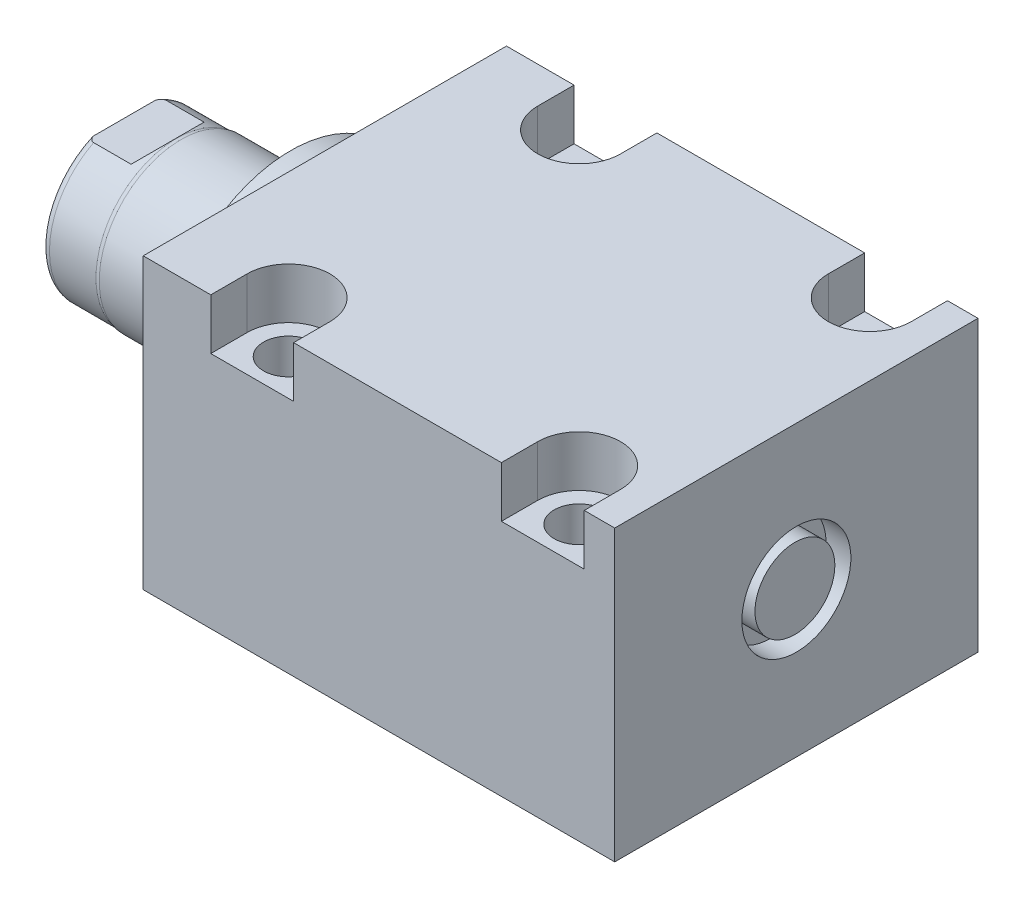
SolidWorks part; units mm, degrees
material "Alloy Steel"
ref_plane "Front Plane" through (0, 0, 0) normal (0, 0, 1) x (1, 0, 0)
ref_plane "Top Plane" through (0, 0, 0) normal (0, 1, 0) x (1, 0, 0)
ref_plane "Right Plane" through (0, 0, 0) normal (1, 0, 0) x (0, 0, -1)
ref_plane "Plane1" through (0, 0, 0) normal (1, 0, 0) x (0, 0, -1)
sketch "Sketch1" plane through (0, 0, 0) normal (1, 0, 0) x (0, 0, -1)
  line L0 (-31.75, 25.146) -> (31.75, 25.146)
  line L1 (31.75, 25.146) -> (31.75, -25.4)
  line L2 (31.75, -25.4) -> (-31.75, -25.4)
  line L3 (-31.75, -25.4) -> (-31.75, 25.146)
  line L4 (0, -24.4475) -> (0, 24.4475) construction
  dimension "D1" = 50.546
  dimension "D2" = 25.4
  dimension "D3" = 63.5
  dimension "D4" = 31.75
extrude "Extrude1" add sketch "Sketch1" along normal blind 82.42
sketch "Sketch5" plane through (0, 0, 0) normal (-1, 0, 0) x (0, 0, 1)
  circle A0 centre (0, 0) radius 22.225
  dimension "D1" = 44.45
extrude "Extrude2" add sketch "Sketch5" along normal blind 5.969
ref_plane "Plane5" through (0, 0, 0) normal (0, -1, 0) x (0, 0, 1)
sketch "Sketch6" plane through (0, 0, 0) normal (0, -1, 0) x (0, 0, 1)
  line L0 (0, 5.969) -> (-14.2875, 5.969)
  line L1 (-14.2875, 5.969) -> (-14.2875, 35.06)
  line L2 (-14.2875, 35.06) -> (0, 35.06)
  line L3 (0, 35.06) -> (0, 5.969)
  line L4 (0, -5.7546) -> (0, 21.1709) construction
  line L5 (22.225, 5.969) -> (-22.225, 5.969) construction
  line L6 (31.75, -82.42) -> (-31.75, -82.42) construction
  dimension "D1" = 117.48
  dimension "D2" = 28.575
revolve "Revolve1" add sketch "Sketch6" angle 360 about L4
ref_plane "Plane6" through (-18.5113, 3.2639, 0) normal (0, 0, 1) x (0, 1, 0)
sketch "S2D0001" plane through (-18.5113, 3.2639, 0) normal (0, 0, 1) x (0, 1, 0)
  line L0 (2.286, 14.481) -> (2.286, -1.9425)
  line L2 (3.4798, 16.5487) -> (-3.2639, 16.5487)
  line L3 (-3.2639, 16.5487) -> (-3.2639, -1.9425)
  line L4 (2.286, 14.481) -> (3.4798, 16.5487)
  line L5 (-3.2639, -18.5113) -> (-3.2639, 2.765) construction
  line L6 (11.0236, 16.5487) -> (-17.5514, 16.5487) construction
  line L7 (2.286, -1.9425) -> (-3.2639, -1.9425)
  dimension "D1" = 30
  dimension "D2" = 13.4874
  dimension "D3" = 11.0998
  dimension "D4" = 18.4912
revolve "Cut-Revolve4" cut sketch "S2D0001" angle 360 about L5
ref_plane "Plane7" through (0, 0, 0) normal (0, 1, 0) x (0, 0, -1)
sketch "Sketch8" plane through (0, 0, 0) normal (0, 1, 0) x (0, 0, -1)
  line L0 (-14.2875, 25.154) -> (-14.097, 25.916)
  line L1 (-14.097, 25.916) -> (-14.097, 34.044)
  line L2 (0, 12.6594) -> (0, 20.8178) construction
  line L3 (-14.2875, 25.154) -> (-14.2875, 35.06)
  line L4 (-13.7089, 35.06) -> (-14.2875, 35.06)
  line L5 (14.2875, 35.06) -> (-14.2875, 35.06) construction
  line L6 (-14.2875, 35.06) -> (-14.2875, 5.969) construction
  arc A0 (-13.7089, 35.06) -> (-14.097, 34.044) centre (-12.573, 34.044) ccw
  dimension "D2" = 1.524
  dimension "D1" = 28.194
  dimension "D3" = 1.016
  dimension "D4" = 0.762
  dimension "D5" = 9.144
revolve "Cut-Revolve5" cut sketch "Sketch8" angle 360 about L2
ref_plane "Plane11" through (0, 0, 0) normal (0, 0, -1) x (0, -1, 0)
sketch "Sketch12" plane through (0, 0, 0) normal (0, 0, -1) x (0, -1, 0)
  line L0 (12.573, 35.06) -> (12.573, 27.4908)
  line L1 (12.573, 27.4908) -> (14.097, 25.9668)
  line L2 (-12.573, 35.06) -> (-12.573, 27.4908)
  line L3 (-12.573, 27.4908) -> (-14.097, 25.9668)
  line L4 (12.573, 35.06) -> (14.097, 35.06)
  line L5 (0, 13.7262) -> (0, 20.767) construction
  line L6 (-14.097, 25.9668) -> (-14.097, 35.06)
  line L8 (14.097, 25.916) -> (14.097, 34.044) construction
  line L9 (14.097, 25.9668) -> (14.097, 35.06)
  line L10 (-12.573, 35.06) -> (-14.097, 35.06)
  line L12 (13.7089, 35.06) -> (-13.7089, 35.06) construction
  dimension "D1" = 25.146
  dimension "D2" = 7.5692
  dimension "D3" = 45
extrude "Cut-Extrude4" cut sketch "Sketch12" against normal mid plane 60.96
hole_wizard "Hole2" positions "Sketch17" profile "Sketch16" legacy
sketch "Sketch17" plane through (0, 25.146, 0) normal (0, 1, 0) x (-1, 0, 0)
  line L0 (0, 0) -> (-59.3363, 0) construction
  line L1 (0, -31.75) -> (0, 31.75) construction
  point P0 (-19.05, -25.4)
  point P9 (-19.05, 25.4)
  dimension "D1" = 50.8
  dimension "D2" = 19.05
sketch "Sketch16" plane through (19.05, 25.146, -25.4) normal (1, 0, 0) x (0, 0, 1)
  line L0 (0, 0) -> (0, 50.546)
  line L1 (0, 50.546) -> (4.3688, 50.546)
  line L2 (4.3688, 50.546) -> (4.3688, 0)
  line L3 (4.3688, 0) -> (0, 0)
  line L4 (0, 110) -> (0, -10) construction
  dimension "Diameter" = 8.7376
  dimension "Depth" = 50.546
pattern_linear "LPattern1" count 2 spacing 50.8 along (1, 0, 0) of "Hole2"
sketch "Sketch18" plane through (0, 25.146, 0) normal (0, 1, 0) x (1, 0, 0)
  line L0 (0, 0) -> (50.053, 0) construction
  line L2 (82.42, -31.75) -> (0, -31.75) construction
  line L4 (77.089, -31.75) -> (62.611, -31.75)
  line L5 (11.811, -25.4) -> (11.811, -31.75)
  line L6 (26.289, -25.4) -> (26.289, -31.75)
  line L7 (62.611, -25.4) -> (62.611, -31.75)
  line L8 (77.089, 25.4) -> (77.089, 31.75)
  line L9 (26.289, -31.75) -> (11.811, -31.75)
  line L12 (26.289, 31.75) -> (11.811, 31.75)
  line L14 (62.611, 25.4) -> (62.611, 31.75)
  line L15 (26.289, 25.4) -> (26.289, 31.75)
  line L16 (11.811, 25.4) -> (11.811, 31.75)
  line L17 (77.089, 31.75) -> (62.611, 31.75)
  line L18 (77.089, -25.4) -> (77.089, -31.75)
  arc A0 (26.289, -25.4) -> (11.811, -25.4) centre (19.05, -25.4) ccw
  arc A1 (77.089, -25.4) -> (62.611, -25.4) centre (69.85, -25.4) ccw
  arc A2 (77.089, 25.4) -> (62.611, 25.4) centre (69.85, 25.4) cw
  arc A3 (26.289, 25.4) -> (11.811, 25.4) centre (19.05, 25.4) cw
  dimension "D1" = 14.478
extrude "Cut-Extrude5" cut sketch "Sketch18" against normal blind 8.89
hole_wizard "Hole3" positions "Sketch20" profile "Sketch19" legacy
sketch "Sketch20" plane through (0, -25.4, 0) normal (0, -1, 0) x (1, 0, 0)
  line L0 (0, 31.75) -> (0, -31.75) construction
  point P0 (12.7, 0)
  dimension "D1" = 12.7
sketch "Sketch19" plane through (12.7, -25.4, 0) normal (1, 0, 0) x (0, 0, -1)
  line L0 (0, 0) -> (0, 10.4789)
  line L1 (0, 10.4789) -> (1.5875, 9.525)
  line L2 (1.5875, 9.525) -> (1.5875, 1.4478)
  line L3 (1.5875, 1.4478) -> (5.6705, 1.4478)
  line L4 (5.6705, 0) -> (0, 0)
  line L5 (0, -11.3109) -> (0, 121.1557) construction
  line L6 (0, 10.4789) -> (-1.5875, 9.525) construction
  line L7 (5.6705, 1.4478) -> (5.6705, 0)
  dimension "Depth" = 9.525
  dimension "Drill Angle" = 118
  dimension "Diameter" = 3.175
  dimension "C-Bore Diameter" = 11.3411
  dimension "C-Bore Depth" = 1.4478
hole_wizard "Hole4" positions "Sketch21" profile "Sketch22" legacy
sketch "Sketch21" plane through (0, -25.4, 0) normal (0, -1, 0) x (1, 0, 0)
  point P0 (63.5, 0)
  dimension "D1" = 50.8
sketch "Sketch22" plane through (63.5, -25.4, 0) normal (1, 0, 0) x (0, 0, -1)
  line L0 (0, 0) -> (0, 10.4789)
  line L1 (0, 10.4789) -> (1.5875, 9.525)
  line L2 (1.5875, 9.525) -> (1.5875, 1.4478)
  line L3 (1.5875, 1.4478) -> (5.6705, 1.4478)
  line L4 (5.6705, 0) -> (0, 0)
  line L5 (0, -11.3109) -> (0, 121.1557) construction
  line L6 (0, 10.4789) -> (-1.5875, 9.525) construction
  line L7 (5.6705, 1.4478) -> (5.6705, 0)
  dimension "Depth" = 9.525
  dimension "Drill Angle" = 118
  dimension "Diameter" = 3.175
  dimension "C-Bore Diameter" = 11.3411
  dimension "C-Bore Depth" = 1.4478
chamfer "Chamfer1" distance 0.635 angle 45 2 edges at (63.5, -23.9522, -1.5875) (12.7, -23.9522, -1.5875)
sketch "Sketch23" plane through (0, 0, 0) normal (0, 0, 1) x (1, 0, 0)
  line L0 (12.7, -23.9522) -> (12.7, -21.4272) construction
  line L1 (10.4775, -23.9522) -> (14.9225, -23.9522) construction
  line L2 (7.0294, -23.9522) -> (18.3705, -23.9522) construction
  line L3 (7.0294, -23.9522) -> (7.0294, -25.4) construction
  circle A0 centre (8.4772, -25.4) radius 1.4478
  dimension "D1" = 2.8956
revolve "Revolve2" add sketch "Sketch23" angle 360 about L0
pattern_linear "LPattern3" count 2 spacing 50.8 along (1, 0, 0) of bodies 128
sketch "Sketch24" plane through (0, 0, 0) normal (0, 0, 1) x (1, 0, 0)
  line L0 (0, 0) -> (74.772, 0) construction
  line L1 (82.42, 9.525) -> (78.102, 9.525)
  line L2 (82.42, 25.146) -> (82.42, -25.4) construction
  line L3 (78.102, 9.525) -> (78.102, 0)
  line L8 (78.102, 0) -> (82.42, 0)
  line L9 (82.42, 0) -> (82.42, 9.525)
  dimension "D1" = 4.318
  dimension "D2" = 19.05
revolve "Cut-Revolve6" cut sketch "Sketch24" angle 360 about L0
sketch "Sketch25" plane through (78.102, 0, 0) normal (1, 0, 0) x (0, 0, -1)
  circle A0 centre (0, 0) radius 6.985
  circle A1 centre (0, 0) radius 9.525 construction
  dimension "D1" = 13.97
extrude "Extrude3" add sketch "Sketch25" along normal blind 4.064
